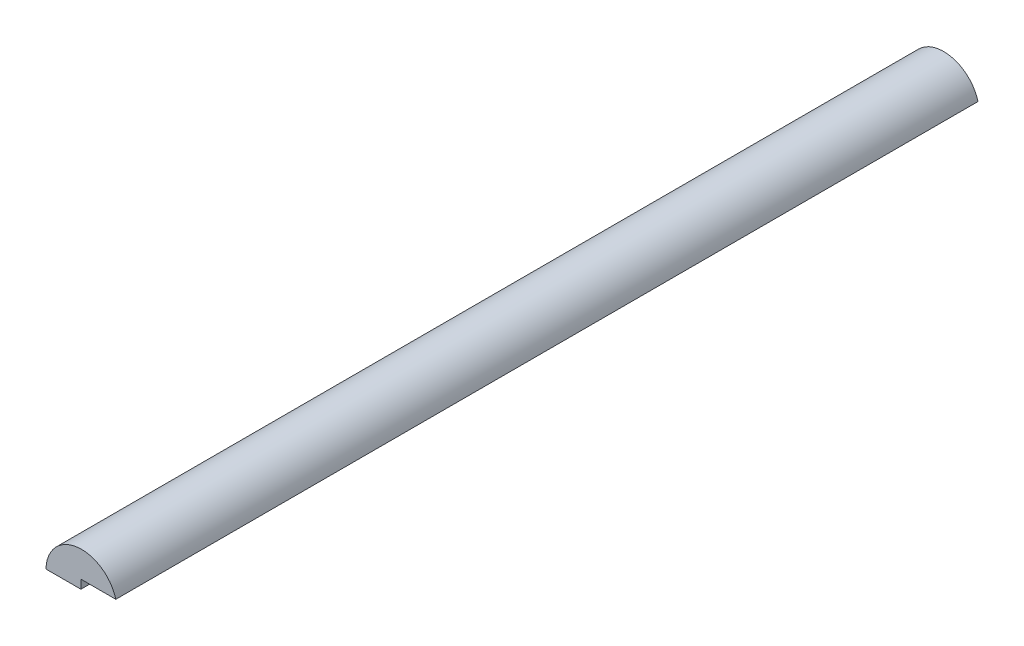
SolidWorks part; units mm, degrees
material "Acrylic (Medium-high impact)"
ref_plane "Front Plane" through (0, 0, 0) normal (0, 0, 1) x (1, 0, 0)
ref_plane "Top Plane" through (0, 0, 0) normal (0, 1, 0) x (1, 0, 0)
ref_plane "Right Plane" through (0, 0, 0) normal (1, 0, 0) x (0, 0, -1)
sketch "Sketch1" plane through (0, 0, 0) normal (0, 0, 1) x (1, 0, 0)
  line L0 (0, 0) -> (0, -0.25)
  line L1 (0, -0.25) -> (-1, -0.25)
  line L2 (0, 0) -> (1, 0)
  line L4 (0.0179, 0.75) -> (-1.893, 0.75) construction
  arc A0 (1, 0) -> (-1, -0.25) centre (0.0179, -0.268) ccw
  dimension "D1" = 0.25
  dimension "D2" = 1
  dimension "D3" = 1
  dimension "D4" = 0.75
extrude "Boss-Extrude1" add sketch "Sketch1" along normal mid plane 24.7
